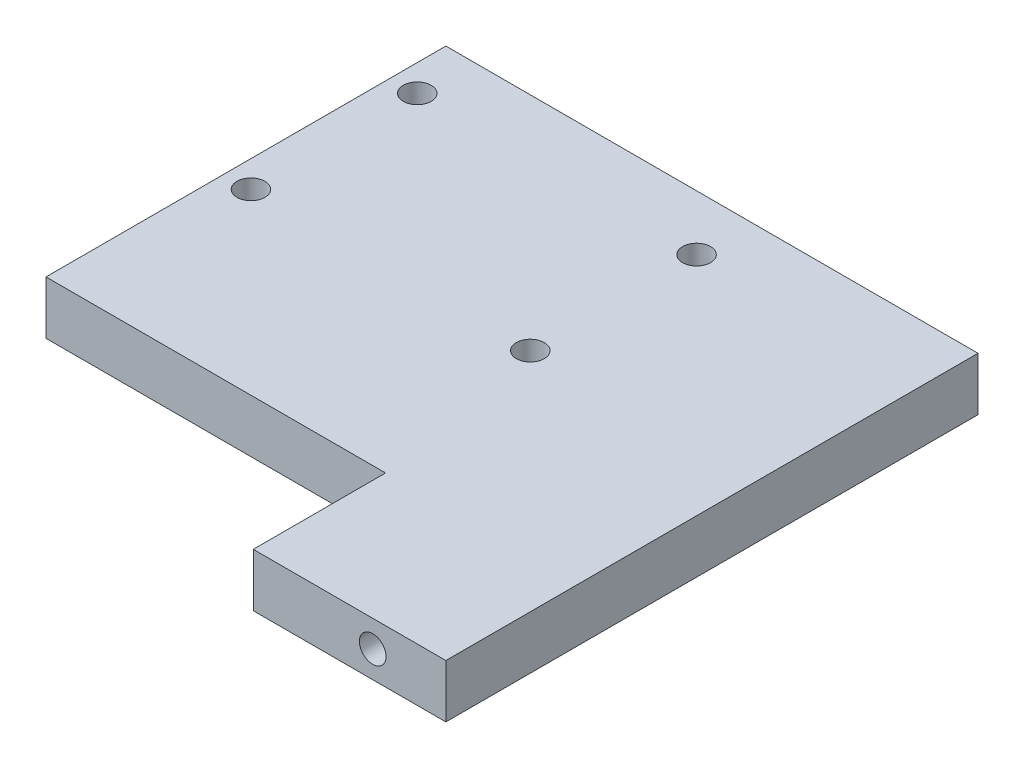
SolidWorks part; units mm, degrees
ref_plane "Front Plane" through (0, 0, 0) normal (0, 0, 1) x (1, 0, 0)
ref_plane "Top Plane" through (0, 0, 0) normal (0, 1, 0) x (1, 0, 0)
ref_plane "Right Plane" through (0, 0, 0) normal (1, 0, 0) x (0, 0, -1)
sketch "Sketch1" plane through (0, 0, 0) normal (0, 1, 0) x (1, 0, 0)
  line L1 (-20, -20) -> (20, -20)
  line L2 (-20, -20) -> (-20, 20)
  line L3 (-20, 20) -> (20, 20)
  line L4 (20, -20) -> (20, 20)
  line L5 (-20, -20) -> (20, 20) construction
  line L6 (-20, 20) -> (20, -20) construction
  point P0 (0, 0)
extrude "Boss-Extrude1" add sketch "Sketch1" along normal blind 4
ref_plane "Plane1" through (0, 4, 0) normal (0, 1, 0) x (1, 0, 0)
ref_plane "Plane2" through (0, 0, -20) normal (0, 0, -1) x (-1, 0, 0)
sketch "Sketch4" plane through (0, 0, 20) normal (0, 0, 1) x (1, 0, 0)
  line L0 (-20, 2) -> (-14.5, 2) construction
  line L1 (-20, 4) -> (-20, 0) construction
  line L2 (20, 2) -> (14.5, 2) construction
  line L3 (20, 4) -> (20, 0) construction
  circle A0 centre (-14.5, 2) radius 1
  circle A1 centre (14.5, 2) radius 1
extrude "Cut-Extrude2" cut sketch "Sketch4" against normal blind 2
sketch "Sketch5" plane through (0, 0, -20) normal (0, 0, -1) x (-1, 0, 0)
  line L0 (-20, 2) -> (-14.5, 2) construction
  line L1 (-20, 4) -> (-20, 0) construction
  line L2 (20, 2) -> (14.5, 2) construction
  line L3 (20, 4) -> (20, 0) construction
  circle A0 centre (-14.5, 2) radius 1
  circle A1 centre (14.5, 2) radius 1
extrude "Cut-Extrude3" cut sketch "Sketch5" against normal blind 2
ref_plane "Plane3" through (0, 0, 0) normal (0, -1, 0) x (-1, 0, 0)
sketch "Sketch6" plane through (0, 0, 0) normal (0, -1, 0) x (-1, 0, 0)
  line L0 (-21.581, 0) -> (21.581, 0) construction
  line L1 (0, 28.2231) -> (0, -28.2231) construction
  line L2 (-5, 17.8472) -> (-2.9989, 15.8461) construction
  line L3 (-5, 0.1233) -> (-5, 17.8472)
  line L4 (20, 0.1233) -> (20, 17.8472)
  line L5 (-5, 17.8472) -> (20, 17.8472)
  line L6 (20, -267.9041) -> (20, 17.8472) construction
  line L7 (20, 17.8472) -> (17.9989, 15.8461) construction
  line L8 (-5, 17.8472) -> (-2.9989, 15.8461) construction
  line L9 (-2.9989, 15.8461) -> (-2.9989, 3.3461) construction
  line L10 (17.9989, 15.8461) -> (17.9989, 3.3461) construction
  line L11 (20, 20) -> (20, -20) construction
  line L13 (-5, 0.1233) -> (20, 0.1233)
  circle A0 centre (17.9989, 15.8461) radius 1.05
  circle A1 centre (-2.9989, 15.8461) radius 1.05
  circle A2 centre (-2.9989, 3.3461) radius 1.05
  circle A3 centre (17.9989, 3.3461) radius 1.05
  point P0 (-3.4386, 0)
  point P4 (0, 0)
  point P7 (0, 0)
extrude "Boss-Extrude3" add sketch "Sketch6" along normal blind 1
sketch "Sketch8" plane through (0, -1, 0) normal (0, -1, 0) x (1, 0, 0)
  circle A0 centre (-17.9989, -15.8461) radius 1.05
  circle A1 centre (2.9989, -15.8461) radius 1.05
  circle A2 centre (2.9989, -3.3461) radius 1.05
  circle A3 centre (-17.9989, -3.3461) radius 1.05
extrude "Cut-Extrude4" cut sketch "Sketch8" against normal through all
sketch "Sketch9" plane through (0, 0, 0) normal (0, -1, 0) x (-1, 0, 0)
  line L0 (20, -0.0583) -> (20, -10.0583) construction
  line L1 (20, 0.1233) -> (20, -20) construction
  line L3 (20, -10.0583) -> (-5.5238, -10.0583)
  line L4 (20, -10.0583) -> (20, -20)
  line L5 (20, -20) -> (-5.5238, -20)
  line L6 (-5.5238, -10.0583) -> (-5.5238, -20)
  line L7 (20, -20) -> (-20, -20) construction
extrude "Cut-Extrude5" cut sketch "Sketch9" against normal through all
